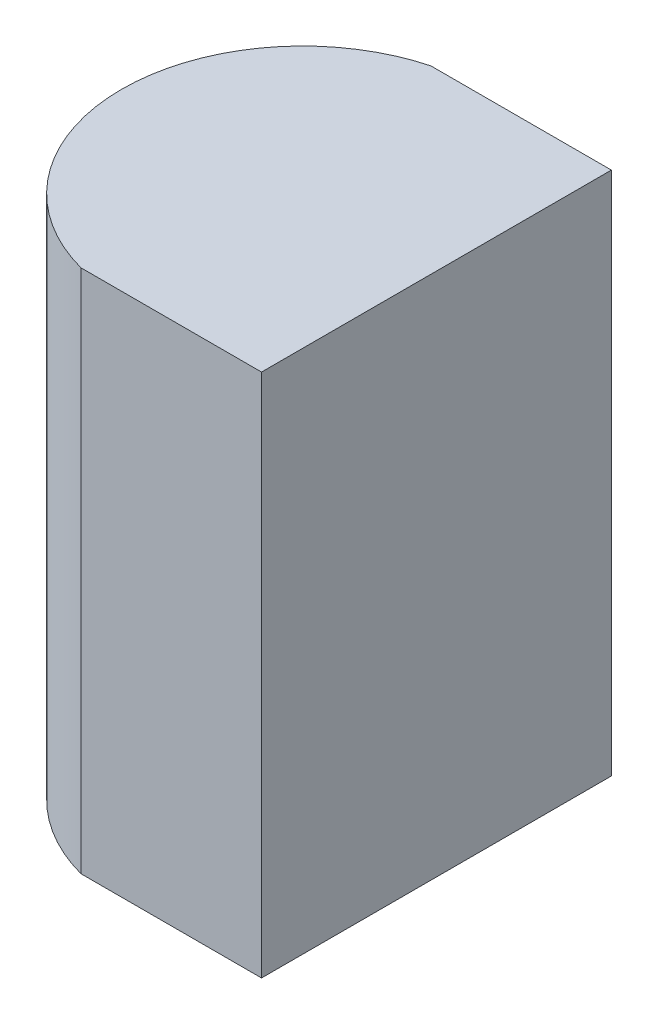
SolidWorks part; units mm, degrees
ref_plane "前视基准面" through (0, 0, 0) normal (0, 0, 1) x (1, 0, 0)
ref_plane "上视基准面" through (0, 0, 0) normal (0, 1, 0) x (1, 0, 0)
ref_plane "右视基准面" through (0, 0, 0) normal (1, 0, 0) x (0, 0, -1)
sketch "草图1" plane through (0, 0, 0) normal (0, 1, 0) x (1, 0, 0)
  line L0 (0, 0) -> (0, -4)
  line L1 (0, 0) -> (-2.0638, 0)
  line L2 (0, -4) -> (-2.0638, -4)
  line L3 (0, -2) -> (6.7931, -2) construction
  arc A0 (-2.0638, 0) -> (-2.0638, -4) centre (-1.53, -2) ccw
  point P7 (-3.6, -2)
  dimension "D2" = 2.07
  dimension "D3" = 3.6
  dimension "D1" = 4
extrude "凸台-拉伸1" add sketch "草图1" along normal blind 6
